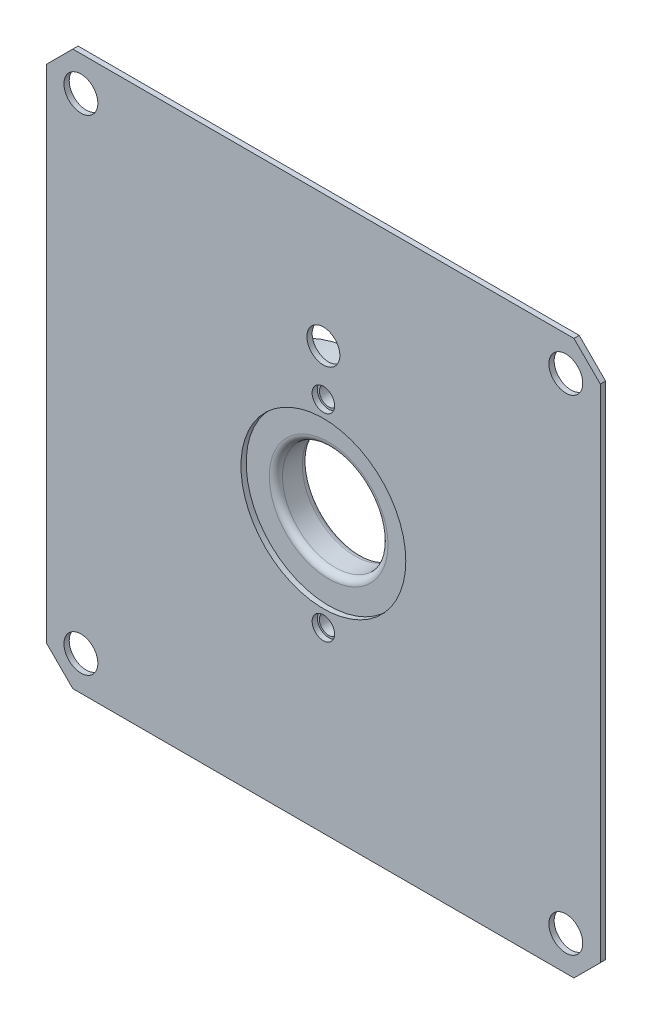
SolidWorks part; units mm, degrees
ref_plane "Front Plane" through (0, 0, 0) normal (0, 0, 1) x (1, 0, 0)
ref_plane "Top Plane" through (0, 0, 0) normal (0, 1, 0) x (1, 0, 0)
ref_plane "Right Plane" through (0, 0, 0) normal (1, 0, 0) x (0, 0, -1)
sketch "Sketch1" plane through (0, 0, 0) normal (0, 0, 1) x (1, 0, 0)
  circle A0 centre (0, 0) radius 11.43
  circle A1 centre (0, 0) radius 5.08
  dimension "D1" = 22.86
  dimension "D2" = 6.35
extrude "Boss-Extrude1" add sketch "Sketch1" along normal blind 3.175
fillet "Fillet1" radius 0.635 2 edges at (5.08, 0, 0) (5.08, 0, 3.175)
hole_wizard "#2-56 Tapped Hole1" positions "Sketch2" profile "Sketch3" tap size "#2-56" standard "ANSI Inch" end condition through all
sketch "Sketch2" plane through (0, 0, 3.175) normal (0, 0, 1) x (1, 0, 0)
  point P0 (0, 9.525)
  dimension "D1" = 9.525
sketch "Sketch3" plane through (0, 9.525, 3.175) normal (1, 0, 0) x (0, -1, 0)
  line L0 (0, 0) -> (0, 3.175)
  line L1 (0, 3.175) -> (0.889, 3.175)
  line L2 (0.889, 3.175) -> (0.889, 0)
  line L5 (0.889, 0) -> (0, 0)
  line L11 (0, -6.35) -> (0, 107.95) construction
  dimension "Thru Tap Drill Dia." = 1.778
  dimension "Thru Tap Drill Depth" = 3.175
cosmetic thread "Hole Thread1" parameters "D2"=2.1844
mirror "Mirror1" about plane through (0, 0, 0) normal (0, 1, 0) of "#2-56 Tapped Hole1"
sketch "Sketch4" plane through (0, 0, 3.175) normal (0, 0, 1) x (1, 0, 0)
  line L1 (-26.67, 26.67) -> (26.67, 26.67)
  line L2 (-26.67, 26.67) -> (-26.67, -26.67)
  line L3 (-26.67, -26.67) -> (26.67, -26.67)
  line L4 (26.67, 26.67) -> (26.67, -26.67)
  circle A0 centre (0, 0) radius 7.9375
  circle A1 centre (0, 9.525) radius 1.0848
  circle A2 centre (0, -9.525) radius 1.0804
  dimension "D5" = 15.875
  dimension "D1" = 53.34
  dimension "D2" = 26.67
  dimension "D3" = 53.34
  dimension "D4" = 26.67
extrude "Boss-Extrude2" add sketch "Sketch4" along normal blind 0.508
hole_wizard "#4 Clearance Hole1" positions "Sketch7" profile "Sketch8" hole size "#4" standard "ANSI Inch" end condition through all
sketch "Sketch7" plane through (0, 0, 3.175) normal (0, 0, -1) x (-1, 0, 0)
  line L0 (0, 0) -> (0, -32.8218) construction
  line L3 (0, 0) -> (-19.4882, -19.4882) construction
  point P0 (-23.3487, -23.3487)
  dimension "D1" = 45
  dimension "D2" = 33.02
sketch "Sketch8" plane through (23.3487, -23.3487, 3.175) normal (1, 0, 0) x (0, 1, 0)
  line L0 (0, 0) -> (0, 0.508)
  line L1 (0, 0.508) -> (1.6319, 0.508)
  line L2 (1.6319, 0.508) -> (1.6319, 0)
  line L5 (1.6319, 0) -> (0, 0)
  line L11 (0, -6.35) -> (0, 107.95) construction
  dimension "Thru Hole Dia." = 3.2639
  dimension "Thru Hole Depth" = 0.508
pattern_circular "CirPattern1" count 4 over 360 about axis through (0, 0, 0) along (0, 0, 1) of "#4 Clearance Hole1"
sketch "Sketch9" plane through (0, 0, 3.683) normal (0, 0, 1) x (1, 0, 0)
  circle A0 centre (0, 13.97) radius 1.5875
  dimension "D1" = 3.175
  dimension "D2" = 13.97
extrude "Cut-Extrude1" cut sketch "Sketch9" against normal blind 0.508
chamfer "Chamfer1" distance 2.54 angle 45 4 edges at (26.67, 26.67, 3.429) (-26.67, 26.67, 3.429) (-26.67, -26.67, 3.429) (26.67, -26.67, 3.429)
equation "\"D2@Sketch4\"=\"D1@Sketch4\"/2"
equation "\"D3@Sketch4\"=\"D1@Sketch4\""
equation "\"D4@Sketch4\"=\"D2@Sketch4\""
